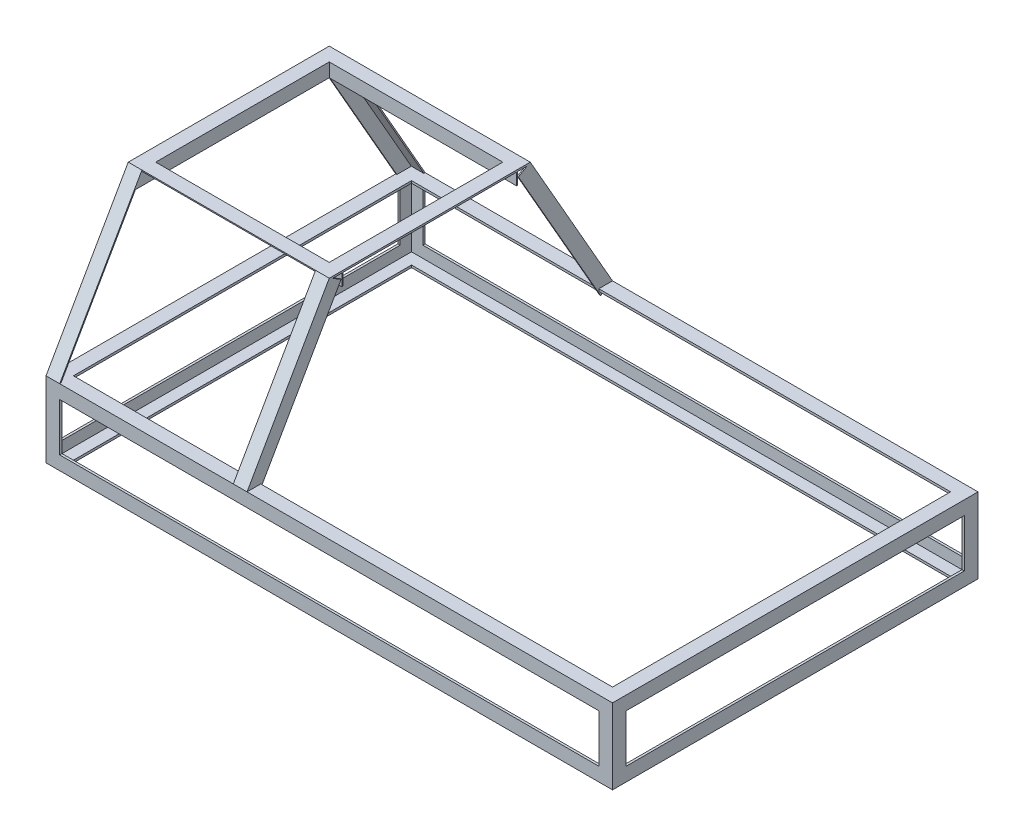
SolidWorks part; units mm, degrees
material "6061 Alloy"
ref_plane "Front Plane" through (0, 0, 0) normal (0, 0, 1) x (1, 0, 0)
ref_plane "Top Plane" through (0, 0, 0) normal (0, 1, 0) x (1, 0, 0)
ref_plane "Right Plane" through (0, 0, 0) normal (1, 0, 0) x (0, 0, -1)
other "Center of Mass"
sketch "Sketch2" plane through (0, 0, 0) normal (1, 0, 0) x (0, 0, -1)
  line L0 (-504.825, -346.075) -> (-504.825, -422.275)
  line L1 (504.825, -422.275) -> (-504.825, -422.275) construction
  line L2 (504.825, -422.275) -> (504.825, 422.275) construction
  line L3 (504.825, 422.275) -> (-504.825, 422.275) construction
  line L4 (-504.825, -422.275) -> (-504.825, 422.275) construction
  line L5 (504.825, -422.275) -> (-504.825, 422.275) construction
  line L6 (504.825, 422.275) -> (-504.825, -422.275) construction
  line L7 (-504.825, -422.275) -> (-428.625, -422.275)
  line L8 (-428.625, -422.275) -> (-428.625, -417.195)
  line L9 (-428.625, -417.195) -> (-498.7519, -417.195)
  line L10 (-498.7519, -417.195) -> (-498.7519, -346.075)
  line L11 (-498.7519, -346.075) -> (-504.825, -346.075)
  line L12 (0, 0) -> (0, -148.4726) construction
  line L13 (0, 0) -> (158.633, 0) construction
  line L14 (498.7519, -417.195) -> (498.7519, -346.075)
  line L15 (428.625, -417.195) -> (498.7519, -417.195)
  line L16 (428.625, -422.275) -> (428.625, -417.195)
  line L17 (504.825, -422.275) -> (428.625, -422.275)
  line L18 (504.825, -346.075) -> (504.825, -422.275)
  line L19 (498.7519, -346.075) -> (504.825, -346.075)
  line L20 (428.625, 417.195) -> (498.7519, 417.195)
  line L21 (428.625, 422.275) -> (428.625, 417.195)
  line L22 (504.825, 422.275) -> (428.625, 422.275)
  line L23 (504.825, 346.075) -> (504.825, 422.275)
  line L24 (498.7519, 346.075) -> (504.825, 346.075)
  line L25 (498.7519, 417.195) -> (498.7519, 346.075)
  line L26 (-498.7519, 417.195) -> (-498.7519, 346.075)
  line L27 (-428.625, 417.195) -> (-498.7519, 417.195)
  line L28 (-428.625, 422.275) -> (-428.625, 417.195)
  line L29 (-504.825, 422.275) -> (-428.625, 422.275)
  line L30 (-504.825, 346.075) -> (-504.825, 422.275)
  line L31 (-498.7519, 346.075) -> (-504.825, 346.075)
  point P0 (0, 0)
  dimension "D1" = 1009.65
  dimension "D2" = 844.55
  dimension "D3" = 76.2
  dimension "D4" = 5.08
extrude "OAL Lenth" [suppressed] add sketch "Sketch2" along normal blind 1574.8
sketch "Sketch3" [suppressed] plane through (0, 0, 0) normal (0, 0, 1) x (1, 0, 0)
  line L0 (0, -422.275) -> (0, -346.075)
  line L1 (1574.8, -346.075) -> (0, -346.075) construction
  line L2 (0, -346.075) -> (0, -422.275) construction
  line L3 (0, -346.075) -> (5.08, -346.075)
  line L4 (5.08, -346.075) -> (5.08, -417.195)
  line L5 (5.08, -417.195) -> (76.2, -417.195)
  line L6 (76.2, -417.195) -> (76.2, -422.275)
  line L7 (1574.8, -422.275) -> (0, -422.275) construction
  line L8 (76.2, -422.275) -> (0, -422.275)
  line L9 (0, 0) -> (697.1877, 0) construction
  line L10 (787.4, 346.075) -> (787.4, -346.075) construction
  line L11 (1574.8, 346.075) -> (0, 346.075) construction
  line L12 (76.2, 422.275) -> (0, 422.275)
  line L13 (76.2, 417.195) -> (76.2, 422.275)
  line L14 (5.08, 417.195) -> (76.2, 417.195)
  line L15 (5.08, 346.075) -> (5.08, 417.195)
  line L16 (0, 346.075) -> (5.08, 346.075)
  line L17 (0, 422.275) -> (0, 346.075)
  line L18 (1574.8, 422.275) -> (1574.8, 346.075)
  line L19 (1574.8, 346.075) -> (1569.72, 346.075)
  line L20 (1569.72, 346.075) -> (1569.72, 417.195)
  line L21 (1569.72, 417.195) -> (1498.6, 417.195)
  line L22 (1498.6, 417.195) -> (1498.6, 422.275)
  line L23 (1498.6, 422.275) -> (1574.8, 422.275)
  line L24 (1498.6, -422.275) -> (1574.8, -422.275)
  line L25 (1498.6, -417.195) -> (1498.6, -422.275)
  line L26 (1569.72, -417.195) -> (1498.6, -417.195)
  line L27 (1569.72, -346.075) -> (1569.72, -417.195)
  line L28 (1574.8, -346.075) -> (1569.72, -346.075)
  line L29 (1574.8, -422.275) -> (1574.8, -346.075)
  dimension "D1" = 5.08
extrude "OAL Width" [suppressed] add sketch "Sketch3" along normal up to surface and the other way up to surface
sketch "Sketch4" [suppressed] plane through (0, 422.275, 0) normal (0, 1, 0) x (1, 0, 0)
  line L0 (0, 504.825) -> (0, 428.625)
  line L1 (0, -428.625) -> (0, -504.825) construction
  line L2 (0, 428.625) -> (5.08, 428.625)
  line L3 (5.08, 428.625) -> (5.08, 499.745)
  line L4 (5.08, 499.745) -> (76.2, 499.745)
  line L5 (76.2, 499.745) -> (76.2, 504.825)
  line L6 (0, 504.825) -> (1574.8, 504.825) construction
  line L7 (76.2, 504.825) -> (0, 504.825)
  line L8 (0, 0) -> (1574.8, 0) construction
  line L9 (1574.8, -428.625) -> (1574.8, -504.825) construction
  line L10 (787.4, 0) -> (787.4, 504.825) construction
  line L11 (76.2, -504.825) -> (0, -504.825)
  line L12 (76.2, -499.745) -> (76.2, -504.825)
  line L13 (5.08, -499.745) -> (76.2, -499.745)
  line L14 (5.08, -428.625) -> (5.08, -499.745)
  line L15 (0, -428.625) -> (5.08, -428.625)
  line L16 (0, -504.825) -> (0, -428.625)
  line L17 (1574.8, -504.825) -> (1574.8, -428.625)
  line L18 (1574.8, -428.625) -> (1569.72, -428.625)
  line L19 (1569.72, -428.625) -> (1569.72, -499.745)
  line L20 (1569.72, -499.745) -> (1498.6, -499.745)
  line L21 (1498.6, -499.745) -> (1498.6, -504.825)
  line L22 (1498.6, -504.825) -> (1574.8, -504.825)
  line L23 (1498.6, 504.825) -> (1574.8, 504.825)
  line L24 (1498.6, 499.745) -> (1498.6, 504.825)
  line L25 (1569.72, 499.745) -> (1498.6, 499.745)
  line L26 (1569.72, 428.625) -> (1569.72, 499.745)
  line L27 (1574.8, 428.625) -> (1569.72, 428.625)
  line L28 (1574.8, 504.825) -> (1574.8, 428.625)
  dimension "D1" = 5.08
  dimension "D2" = 76.2
extrude "OAL Height" [suppressed] add sketch "Sketch4" against normal through all
sketch "Sketch5" plane through (0, 0, 0) normal (1, 0, 0) x (0, 0, -1)
  line L0 (0, 304.8) -> (0, -304.8) construction
  line L1 (-508, -304.8) -> (508, -304.8) construction
  line L2 (-508, -304.8) -> (-508, -266.7)
  line L3 (-508, -304.8) -> (-469.9, -304.8)
  line L4 (-469.9, -304.8) -> (-469.9, -298.45)
  line L5 (-469.9, -298.45) -> (-501.65, -298.45)
  line L6 (-501.65, -298.45) -> (-501.65, -266.7)
  line L7 (-501.65, -266.7) -> (-508, -266.7)
  line L8 (501.65, -266.7) -> (508, -266.7)
  line L9 (501.65, -298.45) -> (501.65, -266.7)
  line L10 (469.9, -298.45) -> (501.65, -298.45)
  line L11 (469.9, -304.8) -> (469.9, -298.45)
  line L12 (508, -304.8) -> (469.9, -304.8)
  line L13 (508, -304.8) -> (508, -266.7)
  line L14 (0, -200.025) -> (-176.3903, -200.025) construction
  line L15 (-508, -95.25) -> (508, -95.25) construction
  line L16 (508, -95.25) -> (508, -133.35)
  line L17 (508, -95.25) -> (469.9, -95.25)
  line L18 (469.9, -95.25) -> (469.9, -101.6)
  line L19 (469.9, -101.6) -> (501.65, -101.6)
  line L20 (501.65, -101.6) -> (501.65, -133.35)
  line L21 (501.65, -133.35) -> (508, -133.35)
  line L22 (-501.65, -133.35) -> (-508, -133.35)
  line L23 (-501.65, -101.6) -> (-501.65, -133.35)
  line L24 (-469.9, -101.6) -> (-501.65, -101.6)
  line L25 (-469.9, -95.25) -> (-469.9, -101.6)
  line L26 (-508, -95.25) -> (-469.9, -95.25)
  line L27 (-508, -95.25) -> (-508, -133.35)
  point P4 (0, 0)
  point P8 (0, -304.8)
  point P32 (0, -95.25)
  dimension "D1" = 1016
  dimension "D2" = 609.6
  dimension "D3" = 38.1
  dimension "D4" = 6.35
  dimension "D5" = 104.775
extrude "Bottom Horizontal Angle" add sketch "Sketch5" along normal blind 1574.8 separate body
sketch "Sketch6" plane through (0, -304.8, 0) normal (0, -1, 0) x (1, 0, 0)
  line L0 (0, 0) -> (1574.8, 0) construction
  line L1 (1574.8, -508) -> (1574.8, 508) construction
  line L2 (1574.8, -508) -> (1536.7, -508)
  line L3 (1574.8, -508) -> (1574.8, -469.9)
  line L4 (1574.8, -469.9) -> (1568.45, -469.9)
  line L5 (1568.45, -469.9) -> (1568.45, -501.65)
  line L6 (1568.45, -501.65) -> (1536.7, -501.65)
  line L7 (1536.7, -501.65) -> (1536.7, -508)
  line L8 (1536.7, 501.65) -> (1536.7, 508)
  line L9 (1568.45, 501.65) -> (1536.7, 501.65)
  line L10 (1568.45, 469.9) -> (1568.45, 501.65)
  line L11 (1574.8, 469.9) -> (1568.45, 469.9)
  line L12 (1574.8, 508) -> (1574.8, 469.9)
  line L13 (1574.8, 508) -> (1536.7, 508)
  line L15 (787.4, 0) -> (787.4, 197.6325) construction
  line L16 (0, -508) -> (0, 508) construction
  line L17 (0, 508) -> (38.1, 508)
  line L18 (0, 508) -> (0, 469.9)
  line L19 (0, 469.9) -> (6.35, 469.9)
  line L20 (6.35, 469.9) -> (6.35, 501.65)
  line L21 (6.35, 501.65) -> (38.1, 501.65)
  line L22 (38.1, 501.65) -> (38.1, 508)
  line L23 (38.1, -501.65) -> (38.1, -508)
  line L24 (6.35, -501.65) -> (38.1, -501.65)
  line L25 (6.35, -469.9) -> (6.35, -501.65)
  line L26 (0, -469.9) -> (6.35, -469.9)
  line L27 (0, -508) -> (0, -469.9)
  line L28 (0, -508) -> (38.1, -508)
  point P3 (787.4, 0)
  point P6 (1574.8, 0)
  point P32 (0, 0)
  dimension "D1" = 38.1
  dimension "D2" = 6.35
  dimension "D3" = 1016
  dimension "D4" = 1574.8
extrude "Front Vertial Angle" add sketch "Sketch6" against normal blind 209.55
sketch "Sketch12" plane through (0, 0, 0) normal (-1, 0, 0) x (0, 0, 1)
  line L0 (0, -304.8) -> (0, 304.8) construction
  line L1 (0, -304.8) -> (-469.9, -304.8) construction
  line L2 (-279.4, 304.8) -> (279.4, 304.8) construction
  line L3 (279.4, 304.8) -> (508, -95.25)
  line L4 (508, -95.25) -> (322.1581, -95.25)
  line L5 (469.9, -95.25) -> (508, -95.25) construction
  line L6 (508, -95.25) -> (508, -304.8) construction
  point P9 (0, 304.8)
  dimension "D1" = 609.6
  dimension "D2" = 558.8
ref_plane "Plane2" through (0, -95.25, 508) normal (0, -0.8682, 0.4961) x (-1, 0, 0)
sketch "Sketch13" plane through (0, -95.25, 508) normal (0, -0.8682, 0.4961) x (-1, 0, 0)
  line L0 (0, 0) -> (0, 38.1)
  line L1 (0, 485.1743) -> (0, 0) construction
  line L2 (0, 38.1) -> (-3.175, 38.1)
  line L3 (-3.175, 38.1) -> (-3.175, 3.175)
  line L4 (-3.175, 3.175) -> (-38.1, 3.175)
  line L5 (-38.1, 3.175) -> (-38.1, 0)
  line L6 (-1574.8, 0) -> (0, 0) construction
  line L7 (-38.1, 0) -> (0, 0)
  line L8 (0, 0) -> (-558.8, 0) construction
  line L9 (-279.4, 0) -> (-279.4, -79.7814) construction
  line L10 (-520.7, 0) -> (-558.8, 0)
  line L11 (-520.7, 3.175) -> (-520.7, 0)
  line L12 (-555.625, 3.175) -> (-520.7, 3.175)
  line L13 (-555.625, 38.1) -> (-555.625, 3.175)
  line L14 (-558.8, 38.1) -> (-555.625, 38.1)
  line L15 (-558.8, 0) -> (-558.8, 38.1)
  line L16 (-1574.8, 0) -> (0, 0) construction
  dimension "D1" = 3.175
  dimension "D2" = 38.1
  dimension "D3" = 558.8
extrude "Rear Diagonal Angle" add sketch "Sketch13" against normal up to vertex (460.758 mm away) up to point (0, 304.8, 279.4)
sketch "Sketch14" plane through (0, 0, 0) normal (0, 0, 1) x (1, 0, 0)
  line L2 (0, -95.25) -> (558.8, -95.25) construction
  line L3 (279.4, -95.25) -> (279.4, 65.0322) construction
  line L33 (19.05, 304.8) -> (19.05, 340.6213) construction
  line L34 (33.02, 266.7) -> (38.1, 266.7)
  line L35 (38.1, 266.7) -> (38.1, 304.8)
  line L36 (38.1, 304.8) -> (0, 304.8)
  line L37 (0, 304.8) -> (0, 299.72)
  line L38 (0, 299.72) -> (33.02, 299.72)
  line L39 (33.02, 299.72) -> (33.02, 266.7)
  line L40 (539.75, 304.8) -> (539.75, 344.5577) construction
  line L41 (525.78, 299.72) -> (525.78, 266.7)
  line L42 (558.8, 299.72) -> (525.78, 299.72)
  line L43 (558.8, 304.8) -> (558.8, 299.72)
  line L44 (520.7, 304.8) -> (558.8, 304.8)
  line L45 (520.7, 266.7) -> (520.7, 304.8)
  line L46 (525.78, 266.7) -> (520.7, 266.7)
extrude "Rear Top Angle" add sketch "Sketch14" along normal up to next
sketch "Sketch8" plane through (0, 0, 0) normal (-1, 0, 0) x (0, 0, 1)
  line L0 (0, -304.8) -> (0, 304.8) construction
  line L1 (260.35, 304.8) -> (260.35, 350.3266) construction
  line L10 (244.475, 266.7) -> (241.3, 266.7)
  line L11 (244.475, 301.625) -> (244.475, 266.7)
  line L12 (279.4, 301.625) -> (244.475, 301.625)
  line L13 (279.4, 304.8) -> (279.4, 301.625)
  line L14 (241.3, 304.8) -> (279.4, 304.8)
  line L15 (241.3, 304.8) -> (241.3, 266.7)
  point P3 (0, 0)
  point P6 (0, 304.8)
extrude "Rear Top Horizontal Angle" add sketch "Sketch8" against normal up to surface (558.8 mm away) up to face at (558.8, 98.7084, 321.5837)
sketch "Sketch15" plane through (0, 0, 0) normal (0, 0, 1) x (1, 0, 0)
  line L0 (0, -266.7) -> (0, -304.8)
  line L1 (0, -95.25) -> (1574.8, -95.25) construction
  line L2 (787.4, -95.25) -> (787.4, 43.9233) construction
  line L3 (1568.45, -266.7) -> (1574.8, -266.7)
  line L4 (1568.45, -298.45) -> (1568.45, -266.7)
  line L5 (1536.7, -298.45) -> (1568.45, -298.45)
  line L6 (1536.7, -304.8) -> (1536.7, -298.45)
  line L7 (0, -304.8) -> (38.1, -304.8)
  line L8 (38.1, -304.8) -> (38.1, -298.45)
  line L9 (38.1, -298.45) -> (6.35, -298.45)
  line L10 (6.35, -298.45) -> (6.35, -266.7)
  line L11 (6.35, -266.7) -> (0, -266.7)
  line L12 (1574.8, -304.8) -> (1536.7, -304.8)
  line L13 (1574.8, -266.7) -> (1574.8, -304.8)
  line L20 (787.4, -95.25) -> (787.4, -304.8) construction
  line L21 (1574.8, -304.8) -> (0, -304.8) construction
  line L24 (787.4, -200.025) -> (896.4031, -200.025) construction
  line L27 (1574.8, -133.35) -> (1574.8, -95.25)
  line L28 (1574.8, -95.25) -> (1536.7, -95.25)
  line L29 (1536.7, -95.25) -> (1536.7, -101.6)
  line L30 (1536.7, -101.6) -> (1568.45, -101.6)
  line L31 (1568.45, -101.6) -> (1568.45, -133.35)
  line L32 (1568.45, -133.35) -> (1574.8, -133.35)
  line L33 (18.8814, -200.025) -> (113.1502, -200.025) construction
  line L35 (6.35, -133.35) -> (0, -133.35)
  line L36 (6.35, -101.6) -> (6.35, -133.35)
  line L37 (38.1, -101.6) -> (6.35, -101.6)
  line L38 (38.1, -95.25) -> (38.1, -101.6)
  line L39 (0, -95.25) -> (38.1, -95.25)
  line L40 (0, -133.35) -> (0, -95.25)
  dimension "D1" = 38.1
  dimension "D2" = 6.35
extrude "Boss-Extrude9" add sketch "Sketch15" against normal up to surface and the other way up to surface
mirror "Mirror" about plane through (0, 0, 0) normal (0, 0, 1) of bodies 129
